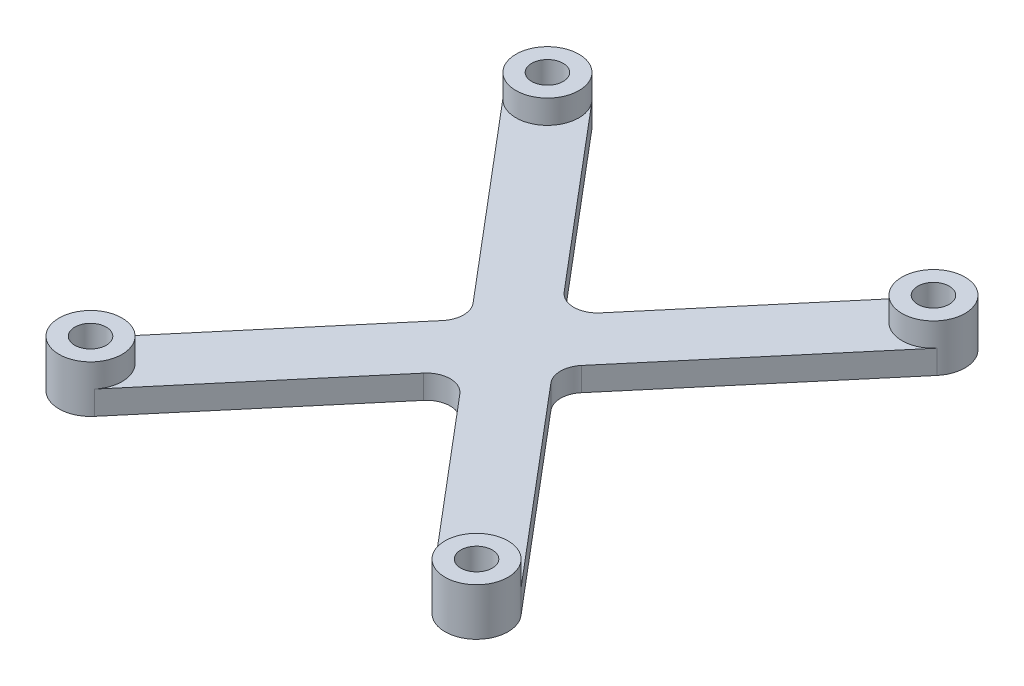
SolidWorks part; units mm, degrees
ref_plane "Front Plane" through (0, 0, 0) normal (0, 0, 1) x (1, 0, 0)
ref_plane "Top Plane" through (0, 0, 0) normal (0, 1, 0) x (1, 0, 0)
ref_plane "Right Plane" through (0, 0, 0) normal (1, 0, 0) x (0, 0, -1)
sketch "Sketch5" plane through (0, 0, 0) normal (0, 1, 0) x (1, 0, 0)
  line L1 (-24.5, -29) -> (24.5, 29) construction
  line L2 (-27.5555, -26.4186) -> (21.4445, 31.5814)
  line L4 (-21.4445, -31.5814) -> (27.5555, 26.4186)
  line L6 (-24.5, 29) -> (24.5, -29) construction
  line L7 (-21.4445, 31.5814) -> (27.5555, -26.4186)
  line L14 (-27.5555, 26.4186) -> (21.4445, -31.5814)
  line L16 (-24.5, 29) -> (24.5, 29) construction
  arc A4 (-27.5555, -26.4186) -> (-21.4445, -31.5814) centre (-24.5, -29) ccw
  arc A5 (27.5555, 26.4186) -> (21.4445, 31.5814) centre (24.5, 29) ccw
  arc A6 (-21.4445, 31.5814) -> (-27.5555, 26.4186) centre (-24.5, 29) ccw
  arc A7 (21.4445, -31.5814) -> (27.5555, -26.4186) centre (24.5, -29) ccw
  point P3 (0, 0)
  point P4 (0, 0)
  point P9 (0, 0)
  point P11 (0, 0)
  dimension "D1" = 49
  dimension "D3" = 4
  dimension "D2" = 58
extrude "Boss-Extrude3" add sketch "Sketch5" along normal blind 3 contours L7 A6 L14 L2 | L14 A7 L7 L4 | L4 A5 L2 L7 | L2 A4 L4 L14 | L2 L14 L4 L7
fillet "Fillet2" radius 3 4 edges at (0, 1.5, -6.1982) (-5.2364, 1.5, 0) (0, 1.5, 6.1982) (5.2364, 1.5, 0)
sketch "Sketch6" plane through (0, 3, 0) normal (0, 1, 0) x (1, 0, 0)
  circle A0 centre (-24.5, 29) radius 4
  circle A1 centre (24.5, 29) radius 4
  circle A2 centre (-24.5, -29) radius 4
  circle A3 centre (24.5, -29) radius 4
extrude "Boss-Extrude4" add sketch "Sketch6" along normal blind 3
sketch "Sketch7" plane through (0, 6, 0) normal (0, 1, 0) x (1, 0, 0)
  circle A0 centre (-24.5, -29) radius 2
  circle A1 centre (-24.5, 29) radius 2
  circle A2 centre (24.5, 29) radius 2
  circle A3 centre (24.5, -29) radius 2
  dimension "D1" = 4
extrude "Cut-Extrude4" cut sketch "Sketch7" against normal through all
